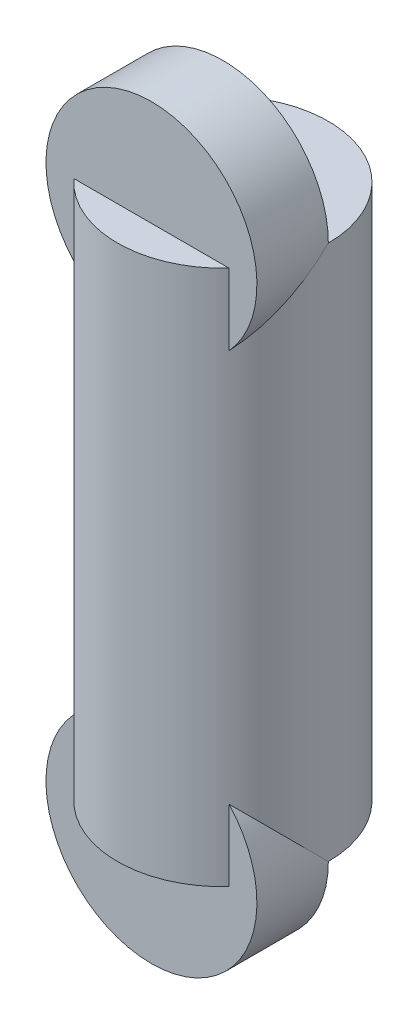
SolidWorks part; units mm, degrees
ref_plane "Front Plane" through (0, 0, 0) normal (0, 0, 1) x (1, 0, 0)
ref_plane "Top Plane" through (0, 0, 0) normal (0, 1, 0) x (1, 0, 0)
ref_plane "Right Plane" through (0, 0, 0) normal (1, 0, 0) x (0, 0, -1)
sketch "Sketch1" plane through (0, 0, 0) normal (0, 0, 1) x (1, 0, 0)
  line L0 (0, 46.0659) -> (0, -33.9341) construction
  line L2 (15.1209, 116.0659) -> (29.5385, 116.0659)
  line L3 (15.1209, 116.0659) -> (15.1209, -33.9341)
  line L4 (15.1209, -33.9341) -> (29.5385, -33.9341)
  line L5 (29.5385, 116.0659) -> (29.5385, -33.9341)
  dimension "D1" = 150
revolve "Revolve1" add sketch "Sketch1" angle 360 about L0
sketch "Sketch2" plane through (0, 0, 0) normal (0, 0, 1) x (1, 0, 0)
  line L0 (-29.5385, -33.9341) -> (29.5385, -33.9341) construction
  line L1 (29.5385, 116.0659) -> (-29.5385, 116.0659) construction
  line L2 (-29.5385, 116.0659) -> (-29.5385, -33.9341) construction
  circle A0 centre (0, 116.0659) radius 29.5385
  circle A1 centre (0, -33.9341) radius 29.5385
extrude "Boss-Extrude1" add sketch "Sketch2" along normal blind 20 contours A0 | A1
